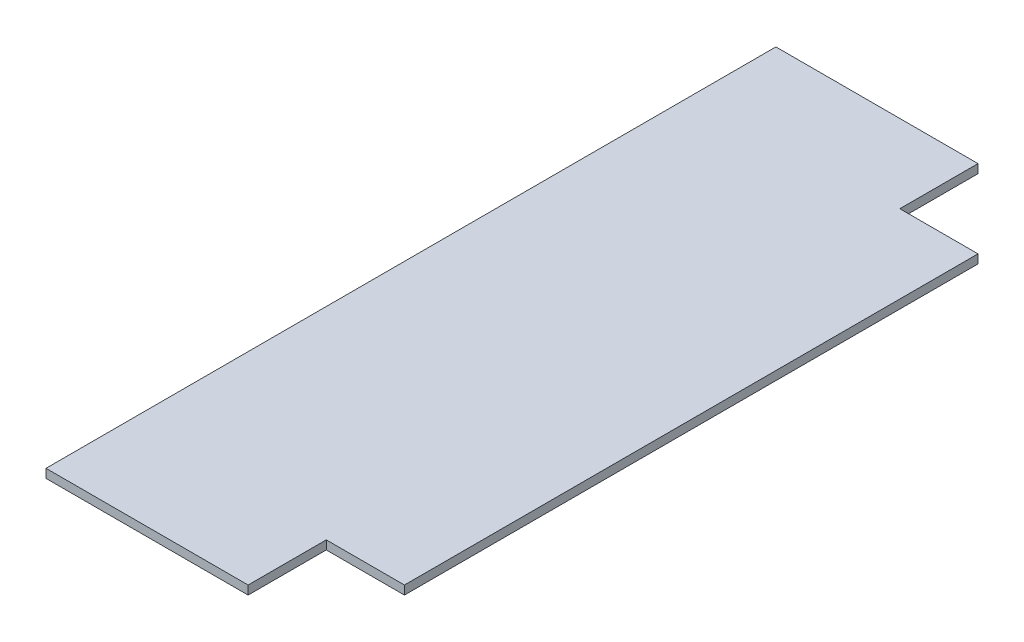
SolidWorks part; units mm, degrees
material "Acrylic (Medium-high impact)"
ref_plane "Front Plane" through (0, 0, 0) normal (0, 0, 1) x (1, 0, 0)
ref_plane "Top Plane" through (0, 0, 0) normal (0, 1, 0) x (1, 0, 0)
ref_plane "Right Plane" through (0, 0, 0) normal (1, 0, 0) x (0, 0, -1)
sketch "Sketch1" plane through (0, 0, 0) normal (0, 1, 0) x (1, 0, 0)
  line L1 (0, 0) -> (152.4, 0)
  line L2 (0, 0) -> (0, -396.875)
  line L3 (0, -396.875) -> (152.4, -396.875)
  line L4 (152.4, 0) -> (152.4, -396.875)
  dimension "D1" = 152.4
  dimension "D2" = 396.875
extrude "Boss-Extrude1" add sketch "Sketch1" along normal blind 4.7625
sketch "Sketch2" plane through (0, 4.7625, 0) normal (0, 1, 0) x (1, 0, 0)
  line L0 (152.4, -20) -> (0, -20) construction
  line L1 (152.4, -396.875) -> (152.4, 0) construction
  line L2 (0, 0) -> (0, -396.875) construction
  line L3 (152.4, 0) -> (0, 0) construction
  line L4 (76.2, 0) -> (76.2, -396.875) construction
  line L5 (0, -396.875) -> (152.4, -396.875) construction
  line L6 (152.4, -198.4375) -> (0, -198.4375) construction
  point P14 (101.2, -20)
  point P15 (51.2, -20)
  point P16 (51.2, -376.875)
  point P17 (101.2, -376.875)
  dimension "D1" = 20
  dimension "D2" = 50
hole_wizard "M4 Clearance Hole1" positions "Sketch2" profile "Sketch3" hole size "M4" standard "ANSI Metric"
sketch "Sketch3" plane through (85, 3.175, 380) normal (1, 0, 0) x (0, 0, 1)
  line L0 (0, 0) -> (0, 3.175)
  line L1 (0, 3.175) -> (2.25, 3.175)
  line L2 (2.25, 3.175) -> (2.25, 0)
  line L5 (2.25, 0) -> (0, 0)
  line L11 (0, -6.35) -> (0, 107.95) construction
  dimension "Thru Hole Dia." = 4.5
  dimension "Thru Hole Depth" = 3.175
sketch "Sketch4" plane through (0, 4.7625, 0) normal (0, 1, 0) x (1, 0, 0)
  line L1 (152.4, 0) -> (109.9, 0)
  line L2 (152.4, 0) -> (152.4, -42.5)
  line L3 (152.4, -42.5) -> (109.9, -42.5)
  line L4 (109.9, 0) -> (109.9, -42.5)
  line L5 (152.4, -396.875) -> (109.9, -396.875)
  line L6 (152.4, -396.875) -> (152.4, -354.375)
  line L7 (152.4, -354.375) -> (109.9, -354.375)
  line L8 (109.9, -396.875) -> (109.9, -354.375)
  dimension "D1" = 42.5
extrude "Cut-Extrude1" cut sketch "Sketch4" against normal through all
